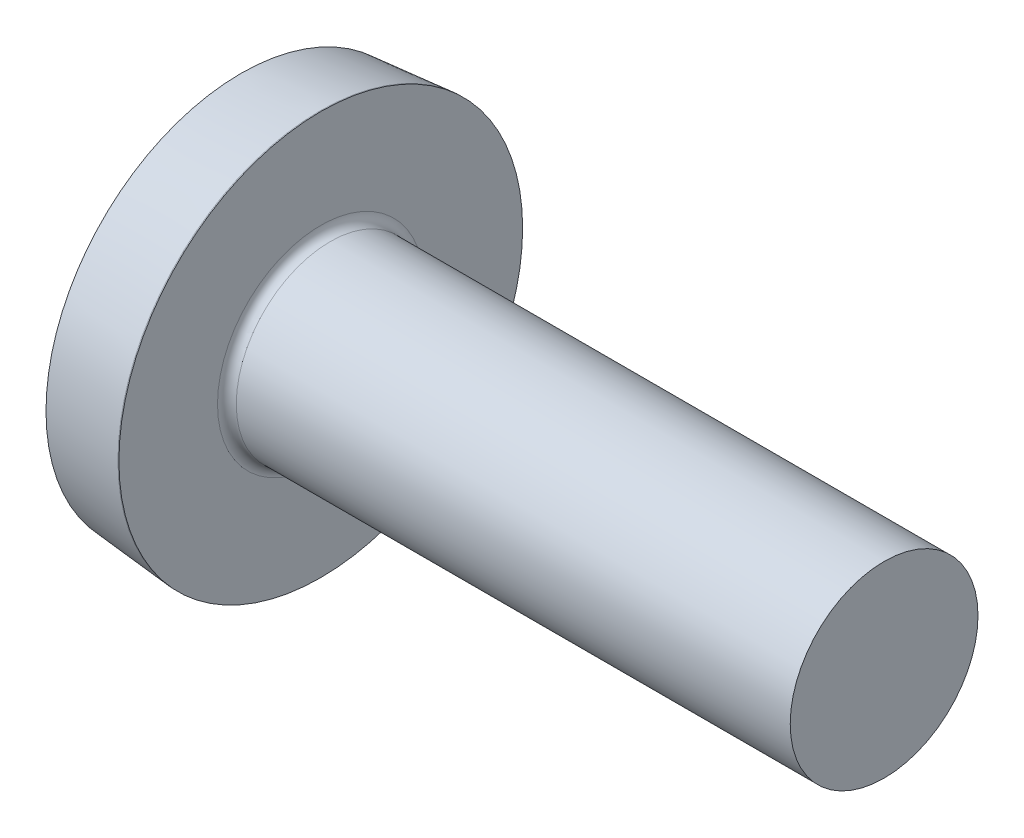
SolidWorks part; units mm, degrees
ref_plane "Plane1" through (0, 0, 0) normal (0, 0, 1) x (1, 0, 0)
ref_plane "Plane2" through (0, 0, 0) normal (0, 1, 0) x (1, 0, 0)
ref_plane "Plane3" through (0, 0, 0) normal (1, 0, 0) x (0, 0, -1)
sketch "BodySke" plane through (0, 0, 0) normal (0, 0, 1) x (1, 0, 0)
  line L0 (1.2, 1) -> (1.2, 2.15)
  line L1 (1.6, 6.35) -> (1.6, -3.175) construction
  line L2 (-25.4, 0) -> (127, 0) construction
  line L3 (7.2, 0) -> (0, 0)
  line L4 (1.2, 1) -> (7.2, 1)
  line L5 (7.2, 1) -> (7.2, 0)
  line L6 (0.35, 2.0765) -> (1.19, 2.15)
  line L8 (1.2, 6.35) -> (1.2, -3.175) construction
  line L9 (1.2, 2.15) -> (1.19, 2.15)
  arc A0 (0.35, 2.0765) -> (0, 0) centre (6.3348, 0) ccw
revolve "Base-Revolve" add sketch "BodySke"
cosmetic thread "ThreadCosmetic" [suppressed]
fillet "Fillet1" radius 0.1 1 edges at (1.2, 0, 1)
sketch "Sketch3" plane through (0, 0, 0) normal (1, 0, 0) x (0, 0, -1)
  line L0 (0.37, -1.1) -> (-0.37, -1.1)
  line L1 (0.37, -1.1) -> (0.37, 1.1)
  line L2 (-0.37, 1.1) -> (0.37, 1.1)
  line L3 (-0.37, 1.1) -> (-0.37, -1.1)
ref_plane "Plane4" through (1.01, 0, 0) normal (1, 0, 0) x (0, 0, -1)
sketch "Sketch4" plane through (1.01, 0, 0) normal (1, 0, 0) x (0, 0, -1)
  line L0 (0.37, -0.5964) -> (-0.37, -0.5964)
  line L1 (0.37, -0.5964) -> (0.37, 0.5964)
  line L2 (-0.37, 0.5964) -> (0.37, 0.5964)
  line L3 (-0.37, 0.5964) -> (-0.37, -0.5964)
loft "Recess" cut profiles "Sketch3", "Sketch4"
pattern_circular "RecPat" count 2 every 90 about axis through (0, 0, 0) along (1, 0, 0) of "Recess"
sketch "RecCorSke" plane through (0, 0, 0) normal (0, 0, 1) x (1, 0, 0)
  line L0 (-3.175, 0) -> (15.875, 0) construction
  line L1 (-25.4, 0) -> (127, 0) construction
  line L2 (0, 0) -> (0, 0.6266)
  line L3 (0, 0.6266) -> (1.01, 0.556)
  line L4 (1.01, 0.556) -> (1.1907, 0)
  line L5 (1.1907, 0) -> (0, 0)
revolve "RecessCore" cut sketch "RecCorSke" angle 360 about L0
sketch "ThdSchSke" plane through (0, 0, 0) normal (0, 0, 1) x (1, 0, 0)
  line L0 (2, -0.774) -> (1.8418, -1)
  line L1 (2, -0.774) -> (2.1582, -1)
  line L2 (2.1582, -1) -> (2.1582, -1.25)
  line L3 (-3.175, 0) -> (5.1513, 0) construction
  line L5 (2.1582, -1.25) -> (1.8418, -1.25)
  line L6 (1.8418, -1.25) -> (1.8418, -1)
revolve "ThreadSchematic" [suppressed] cut sketch "ThdSchSke" angle 360 about L3
pattern_linear "ThdSchPat" [suppressed]
equation "' \"Diameter@BodySke\" = 8"
equation "' \"Length@BodySke\" = 35"
equation "' \"Head_dia@BodySke\" = 16.4"
equation "' \"Oval_ht@BodySke\" = 1.7"
equation "' \"Head_ht@BodySke\" = 4.8"
equation "' \"Thread_nom@BodySke\" =  30"
equation "' \"Thread_nom@BodySke\" = 30"
equation "' \"Head_ang@BodySke\" = 85"
equation "' \"Cross_dia@Sketch3\" = 7.8"
equation "' \"Cross_width@Sketch3\" = 1.42"
equation "' \"Cross_depth@Plane4\" = 4.36"
equation "' \"Diameter@RecCorSke\" = 2.561"
equation "' \"Radius@Fillet1\" = 0.4"
equation "' \"Thread_minor@ThreadCosmetic\" = 6.619"
equation "' \"Advance@BodySke\" = 1.25"
equation "\"D1@Sketch3\" = \"Cross_dia@Sketch3\" / 2"
equation "\"D2@Sketch3\" = \"Cross_width@Sketch3\" / 2"
equation "\"Depth@RecCorSke\" = \"Cross_depth@Plane4\""
equation "\"D1@Sketch4\" = \"Cross_width@Sketch3\""
equation "\"D2@Sketch4\" = \"Cross_dia@Sketch3\" - 2.0 * \"Cross_depth@Plane4\" * tan(26.5  * 0.017453292)"
equation "\"D3@Sketch4\" = \"D1@Sketch4\" / 2"
equation "\"D4@Sketch4\" = \"D2@Sketch4\" / 2"
equation "\"Thread_length@ThreadCosmetic\" = ((sgn( (\"Length@BodySke\" - \"Advance@BodySke\" * 2.0 ) - \"Thread_nom@BodySke\" )-1)*( (\"Length@BodySke\" - \"Advance@BodySke\" * 2.0 ) - \"Thread_nom@BodySke\" ))/-2+ \"Thread_nom@BodySke\""
equation "\"Thread_minor@ThdSchSke\" = \"Thread_minor@ThreadCosmetic\""
equation "\"Diameter@ThdSchSke\" = \"Diameter@BodySke\""
equation "\"Overcut@ThdSchSke\" = \"Diameter@BodySke\" * 1.25"
equation "\"Start@ThdSchSke\" = \"Head_ht@BodySke\" + \"Length@BodySke\" - \"Thread_length@ThreadCosmetic\"  '---Non-countersunk---"
equation "\"Num_threads@ThdSchPat\" = int( \"Thread_length@ThreadCosmetic\" / \"Advance@BodySke\" + 0.999 )  + 1"
equation "\"Advance@ThdSchPat\" = \"Thread_length@ThreadCosmetic\" /  (\"Num_threads@ThdSchPat\" - 1) 'relax it"
